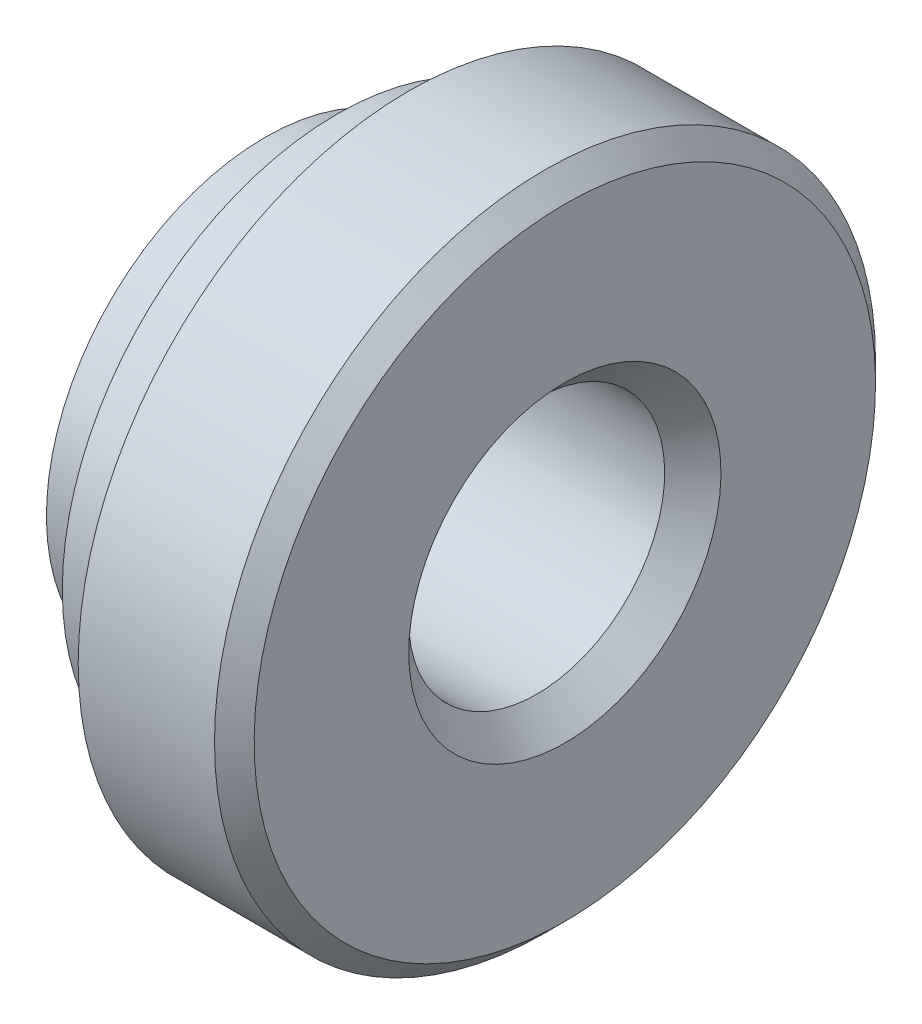
SolidWorks part; units mm, degrees
material "1023 Carbon Steel Sheet (SS)"
ref_plane "Front Plane" through (0, 0, 0) normal (0, 0, 1) x (1, 0, 0)
ref_plane "Top Plane" through (0, 0, 0) normal (0, 1, 0) x (1, 0, 0)
ref_plane "Right Plane" through (0, 0, 0) normal (1, 0, 0) x (0, 0, -1)
sketch "Sketch1" plane through (0, 0, 0) normal (0, 0, 1) x (1, 0, 0)
  line L0 (0.69, 2.065) -> (0.3185, 2.1)
  line L1 (0.3185, 2.1) -> (0, 2.1)
  line L2 (0, 2.1) -> (0, 1.5)
  line L3 (0, 1.5) -> (0.2705, 1.2295)
  line L4 (0.2705, 1.2295) -> (2.6095, 1.2295)
  line L5 (2.6095, 1.2295) -> (2.88, 1.5)
  line L6 (2.88, 1.5) -> (2.88, 2.9845)
  line L7 (2.88, 2.9845) -> (2.6895, 3.175)
  line L8 (2.6895, 3.175) -> (1.38, 3.175)
  line L9 (1.38, 3.175) -> (1.38, 2.6375)
  line L10 (1.38, 2.6375) -> (0.69, 2.6375)
  line L11 (0.69, 2.6375) -> (0.69, 2.065)
  line L12 (0, 0) -> (2.88, 0) construction
revolve "Revolve1" add sketch "Sketch1" angle 360 about L12
